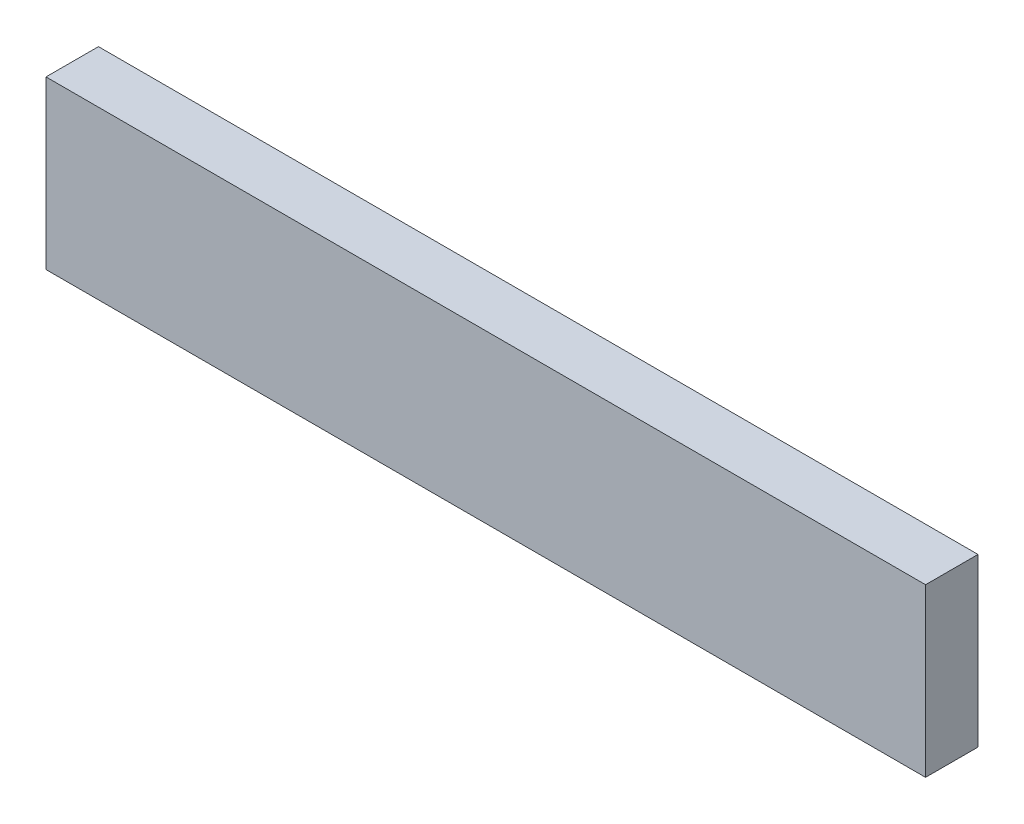
SolidWorks part; units mm, degrees
ref_plane "Plan de face" through (0, 0, 0) normal (0, 0, 1) x (1, 0, 0)
ref_plane "Plan de dessus" through (0, 0, 0) normal (0, 1, 0) x (1, 0, 0)
ref_plane "Plan de droite" through (0, 0, 0) normal (1, 0, 0) x (0, 0, -1)
sketch "Esquisse1" plane through (0, 0, 0) normal (0, 0, 1) x (1, 0, 0)
  line L1 (-184.5, 35) -> (184.5, 35)
  line L2 (-184.5, 35) -> (-184.5, -35)
  line L3 (-184.5, -35) -> (184.5, -35)
  line L4 (184.5, 35) -> (184.5, -35)
  line L5 (-184.5, 35) -> (184.5, -35) construction
  line L6 (-184.5, -35) -> (184.5, 35) construction
  point P0 (0, 0)
  dimension "D1" = 369
  dimension "D2" = 70
extrude "Boss.-Extru.1" add sketch "Esquisse1" along normal blind 22
